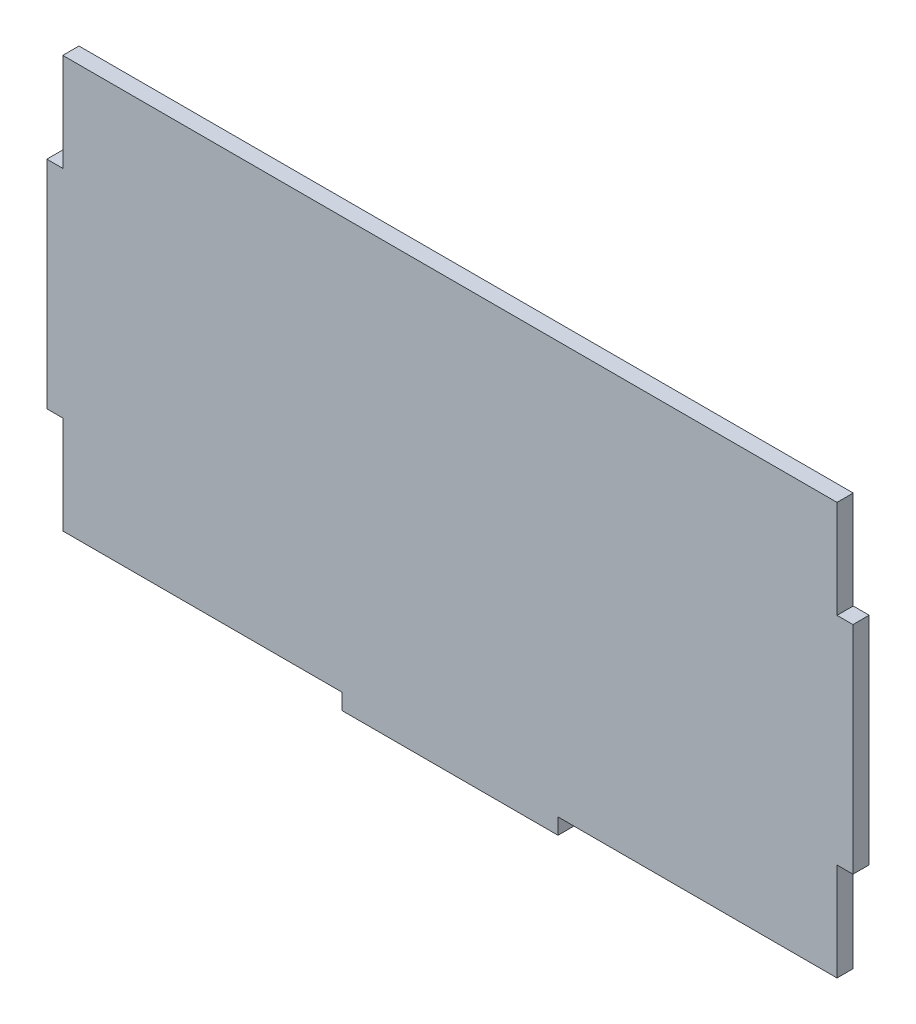
SolidWorks part; units mm, degrees
ref_plane "Front Plane" through (0, 0, 0) normal (0, 0, 1) x (1, 0, 0)
ref_plane "Top Plane" through (0, 0, 0) normal (0, 1, 0) x (1, 0, 0)
ref_plane "Right Plane" through (0, 0, 0) normal (1, 0, 0) x (0, 0, -1)
sketch "Sketch1" plane through (0, 0, 0) normal (0, 0, 1) x (1, 0, 0)
  line L1 (-71.6153, -38.1) -> (71.6153, -38.1)
  line L2 (-71.6153, -38.1) -> (-71.6153, 38.1)
  line L3 (-71.6153, 38.1) -> (71.6153, 38.1)
  line L4 (71.6153, -38.1) -> (71.6153, 38.1)
  line L5 (-71.6153, -38.1) -> (71.6153, 38.1) construction
  line L6 (-71.6153, 38.1) -> (71.6153, -38.1) construction
  point P0 (0, 0)
  dimension "D1" = 76.2
  dimension "D2" = 143.2306
extrude "Boss-Extrude1" add sketch "Sketch1" along normal mid plane 2.9972
sketch "Sketch2" plane through (0, 0, 1.4986) normal (0, 0, 1) x (1, 0, 0)
  line L0 (-71.6153, 38.1) -> (-71.6153, -38.1) construction
  line L1 (-71.6153, 20) -> (-74.5617, 20)
  line L2 (-71.6153, 20) -> (-71.6153, -20)
  line L3 (-71.6153, -20) -> (-74.5617, -20)
  line L4 (-74.5617, 20) -> (-74.5617, -20)
  line L5 (-71.6153, -38.1) -> (71.6153, -38.1) construction
  line L6 (-20, -38.1) -> (20, -38.1)
  line L7 (-20, -38.1) -> (-20, -41.0464)
  line L8 (-20, -41.0464) -> (20, -41.0464)
  line L9 (20, -38.1) -> (20, -41.0464)
  line L10 (71.6153, -38.1) -> (71.6153, 38.1) construction
  line L11 (71.6153, -20) -> (74.5617, -20)
  line L12 (71.6153, -20) -> (71.6153, 20)
  line L13 (71.6153, 20) -> (74.5617, 20)
  line L14 (74.5617, -20) -> (74.5617, 20)
  point P18 (71.6153, 0)
  point P20 (0, -38.1)
  dimension "D1" = 40
  dimension "D2" = 40
  dimension "D3" = 2.9464
extrude "Boss-Extrude2" add sketch "Sketch2" against normal through all
